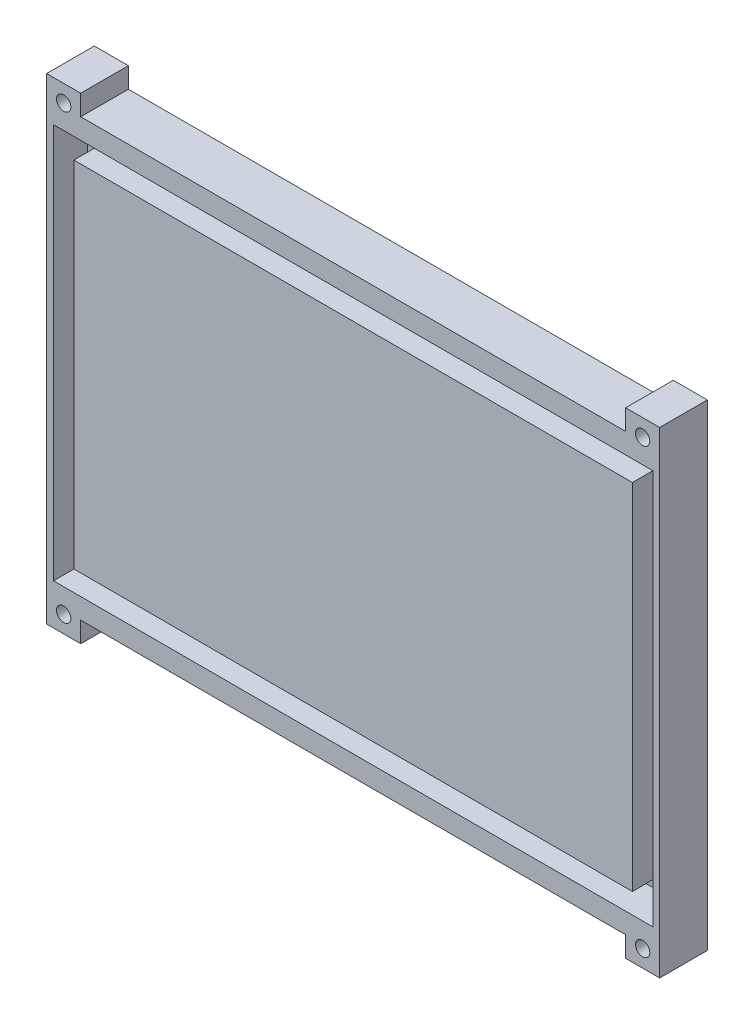
SolidWorks part; units mm, degrees
ref_plane "前基準面" through (0, 0, 0) normal (0, 0, 1) x (1, 0, 0)
ref_plane "上基準面" through (0, 0, 0) normal (0, 1, 0) x (1, 0, 0)
ref_plane "右基準面" through (0, 0, 0) normal (1, 0, 0) x (0, 0, -1)
sketch "草圖1" plane through (0, 0, 0) normal (0, 0, 1) x (1, 0, 0)
  line L1 (-89.0867, 42.9814) -> (10.9133, 42.9814)
  line L2 (-89.0867, 42.9814) -> (-89.0867, -27.0186)
  line L3 (-89.0867, -27.0186) -> (10.9133, -27.0186)
  line L4 (10.9133, 42.9814) -> (10.9133, -27.0186)
  dimension "D1" = 70
  dimension "D2" = 100
extrude "填料-伸長1" add sketch "草圖1" along normal blind 10 contours L4 L3 L2 L1
ref_plane "平面1" through (0, 0, 10) normal (0, 0, 1) x (1, 0, 0)
sketch "草圖6" plane through (0, 0, 10) normal (0, 0, 1) x (1, 0, 0)
  line L0 (-89.0867, 7.9814) -> (10.9133, 7.9814) construction
  line L1 (-89.0867, 42.9814) -> (-89.0867, -27.0186) construction
  line L2 (10.9133, 42.9814) -> (10.9133, -27.0186) construction
  line L3 (-39.0867, 42.9814) -> (-39.0867, -27.0186) construction
  line L4 (-89.0867, 42.9814) -> (10.9133, 42.9814) construction
  line L5 (-89.0867, -27.0186) -> (10.9133, -27.0186) construction
  line L6 (5.9133, 37.9814) -> (0.9133, 37.9814)
  line L7 (-84.0867, 42.9814) -> (-79.0867, 42.9814)
  line L8 (-84.0867, 42.9814) -> (-84.0867, 37.9814)
  line L9 (-84.0867, 37.9814) -> (-79.0867, 37.9814)
  line L10 (-79.0867, 42.9814) -> (-79.0867, 37.9814)
  line L11 (0.9133, 42.9814) -> (0.9133, 37.9814)
  line L12 (5.9133, 42.9814) -> (0.9133, 42.9814)
  line L13 (5.9133, 42.9814) -> (5.9133, 37.9814)
  line L14 (-84.0867, -22.0186) -> (-79.0867, -22.0186)
  line L15 (-79.0867, -27.0186) -> (-79.0867, -22.0186)
  line L16 (-84.0867, -27.0186) -> (-79.0867, -27.0186)
  line L17 (-84.0867, -27.0186) -> (-84.0867, -22.0186)
  line L18 (5.9133, -27.0186) -> (5.9133, -22.0186)
  line L19 (5.9133, -27.0186) -> (0.9133, -27.0186)
  line L20 (0.9133, -27.0186) -> (0.9133, -22.0186)
  line L21 (5.9133, -22.0186) -> (0.9133, -22.0186)
  dimension "D1" = 5
  dimension "D2" = 5
  dimension "D3" = 5
extrude "除料-伸長4" cut sketch "草圖6" against normal blind 5
ref_plane "平面2" through (0, 0, 0) normal (0, 0, -1) x (-1, 0, 0)
sketch "草圖7" plane through (0, 0, 0) normal (0, 0, -1) x (-1, 0, 0)
  line L0 (-10.9133, 7.9814) -> (89.0867, 7.9814) construction
  line L1 (-10.9133, 42.9814) -> (-10.9133, -27.0186) construction
  line L2 (89.0867, 42.9814) -> (89.0867, -27.0186) construction
  line L3 (39.0867, 42.9814) -> (39.0867, -27.0186) construction
  line L4 (89.0867, 42.9814) -> (-10.9133, 42.9814) construction
  line L5 (89.0867, -27.0186) -> (-10.9133, -27.0186) construction
  line L6 (84.0867, 37.9814) -> (79.0867, 37.9814)
  line L7 (-5.9133, 42.9814) -> (-0.9133, 42.9814)
  line L8 (-5.9133, 42.9814) -> (-5.9133, 37.9814)
  line L9 (-5.9133, 37.9814) -> (-0.9133, 37.9814)
  line L10 (-0.9133, 42.9814) -> (-0.9133, 37.9814)
  line L11 (79.0867, 42.9814) -> (79.0867, 37.9814)
  line L12 (84.0867, 42.9814) -> (79.0867, 42.9814)
  line L13 (84.0867, 42.9814) -> (84.0867, 37.9814)
  line L14 (84.0867, -27.0186) -> (84.0867, -22.0186)
  line L15 (84.0867, -27.0186) -> (79.0867, -27.0186)
  line L16 (79.0867, -27.0186) -> (79.0867, -22.0186)
  line L17 (84.0867, -22.0186) -> (79.0867, -22.0186)
  line L18 (-5.9133, -22.0186) -> (-0.9133, -22.0186)
  line L19 (-0.9133, -27.0186) -> (-0.9133, -22.0186)
  line L20 (-5.9133, -27.0186) -> (-0.9133, -27.0186)
  line L21 (-5.9133, -27.0186) -> (-5.9133, -22.0186)
  dimension "D1" = 5
  dimension "D2" = 5
  dimension "D3" = 5
extrude "除料-伸長5" cut sketch "草圖7" against normal blind 3
sketch "草圖8" plane through (0, 0, 0) normal (0, 0, -1) x (-1, 0, 0)
  line L0 (-10.9133, 7.9814) -> (89.0867, 7.9814) construction
  line L1 (-10.9133, 42.9814) -> (-10.9133, -27.0186) construction
  line L2 (89.0867, 42.9814) -> (89.0867, -27.0186) construction
  line L3 (39.0867, 42.9814) -> (39.0867, -27.0186) construction
  line L4 (79.0867, 42.9814) -> (-0.9133, 42.9814) construction
  line L5 (79.0867, -27.0186) -> (-0.9133, -27.0186) construction
  line L6 (-5.9133, 40.4814) -> (-0.9133, 40.4814) construction
  line L7 (-5.9133, 42.9814) -> (-5.9133, 37.9814) construction
  line L8 (-0.9133, 37.9814) -> (-0.9133, 42.9814) construction
  line L9 (-3.4133, 37.9814) -> (-3.4133, 42.9814) construction
  line L10 (-5.9133, 37.9814) -> (-0.9133, 37.9814) construction
  line L11 (-0.9133, 42.9814) -> (-5.9133, 42.9814) construction
  circle A0 centre (-3.4133, 40.4814) radius 1.05
  circle A1 centre (81.5867, 40.4814) radius 1.05
  circle A2 centre (81.5867, -24.5186) radius 1.05
  circle A3 centre (-3.4133, -24.5186) radius 1.05
  dimension "D1" = 2.1
  dimension "D2" = 2.1
  dimension "D3" = 2.1
  dimension "D4" = 2.1
extrude "除料-伸長6" cut sketch "草圖8" against normal blind 42
sketch "草圖10" plane through (0, 0, 0) normal (0, 0, 1) x (1, 0, 0)
  line L1 (-89.0867, 42.9814) -> (10.9133, 42.9814)
  line L2 (-89.0867, 42.9814) -> (-89.0867, -27.0186)
  line L3 (-89.0867, -27.0186) -> (10.9133, -27.0186)
  line L4 (10.9133, 42.9814) -> (10.9133, -27.0186)
extrude "除料-伸長7" cut sketch "草圖10" along normal blind 3
ref_plane "平面3" through (10.9133, 0, 0) normal (1, 0, 0) x (0, 0, -1)
sketch "草圖11" plane through (10.9133, 0, 0) normal (1, 0, 0) x (0, 0, -1)
  line L0 (-10, 38.5) -> (-10, -38.5) construction
  line L1 (-3, 42.9814) -> (-10, 42.9814)
  line L2 (-3, 42.9814) -> (-3, -27.0186)
  line L3 (-3, -27.0186) -> (-10, -27.0186)
  line L4 (-10, 42.9814) -> (-10, -27.0186)
  line L5 (-10, -27.0186) -> (-3, -27.0186) construction
extrude "除料-伸長8" cut sketch "草圖11" against normal blind 5
ref_plane "平面4" through (-89.0867, 0, 0) normal (-1, 0, 0) x (0, 0, 1)
sketch "草圖12" plane through (-89.0867, 0, 0) normal (-1, 0, 0) x (0, 0, 1)
  line L1 (3, 42.9814) -> (10, 42.9814)
  line L2 (3, 42.9814) -> (3, -27.0186)
  line L3 (3, -27.0186) -> (10, -27.0186)
  line L4 (10, 42.9814) -> (10, -27.0186)
extrude "除料-伸長9" cut sketch "草圖12" against normal blind 5
ref_plane "平面5" through (0, 0, 10) normal (0, 0, 1) x (1, 0, 0)
sketch "草圖13" plane through (0, 0, 10) normal (0, 0, 1) x (1, 0, 0)
  line L0 (-39.0867, 42.9814) -> (-39.0867, -27.0186) construction
  line L1 (-84.0867, 37.9814) -> (-79.0867, 37.9814)
  line L2 (-84.0867, 37.9814) -> (-84.0867, -22.0186)
  line L3 (-84.0867, -22.0186) -> (-79.0867, -22.0186)
  line L4 (-79.0867, 37.9814) -> (-79.0867, -22.0186)
  line L5 (-79.0867, 42.9814) -> (0.9133, 42.9814) construction
  line L6 (-79.0867, -27.0186) -> (0.9133, -27.0186) construction
  line L7 (5.9133, -22.0186) -> (0.9133, -22.0186)
  line L8 (0.9133, 37.9814) -> (0.9133, -22.0186)
  line L9 (5.9133, 37.9814) -> (0.9133, 37.9814)
  line L10 (5.9133, 37.9814) -> (5.9133, -22.0186)
sketch "草圖15" plane through (0, 0, 10) normal (0, 0, 1) x (1, 0, 0)
  line L0 (-84.0867, 7.9814) -> (0.9133, 7.9814) construction
  line L1 (-84.0867, 37.9814) -> (-84.0867, -22.0186) construction
  line L2 (0.9133, 37.9814) -> (0.9133, -22.0186) construction
  line L3 (-39.0867, 42.9814) -> (-39.0867, -27.0186) construction
  line L24 (-83.0867, 36.9814) -> (-83.0867, -21.0186)
  line L25 (-83.0867, 36.9814) -> (4.9133, 36.9814)
  line L26 (4.9133, 36.9814) -> (4.9133, -21.0186)
  line L27 (-80.0867, 33.9814) -> (1.9133, 33.9814)
  line L28 (-79.0867, 42.9814) -> (0.9133, 42.9814) construction
  line L29 (5.9133, 37.9814) -> (5.9133, -22.0186) construction
  line L30 (-80.0867, 33.9814) -> (-80.0867, -18.0186)
  line L31 (1.9133, 33.9814) -> (1.9133, -18.0186)
  line L32 (-83.0867, -21.0186) -> (4.9133, -21.0186)
  line L33 (-80.0867, -18.0186) -> (1.9133, -18.0186)
  point P19 (-83.0867, 7.9814)
  point P26 (-0.0867, 7.9814)
  point P27 (1.9133, 7.9814)
  point P29 (-80.0867, 7.9814)
  point P30 (-83.0867, 7.9814)
  point P32 (4.9133, 7.9814)
  point P33 (1.9133, 7.9814)
  point P35 (-80.0867, 7.9814)
  dimension "D1" = 3
  dimension "D2" = 9
  dimension "D3" = 3
  dimension "D4" = 1
  dimension "D5" = 1
  dimension "D6" = 3
  dimension "D7" = 6
extrude "除料-伸長12" cut sketch "草圖15" against normal blind 5
ref_plane "平面6" through (0, 0, 5) normal (0, 0, 1) x (1, 0, 0)
sketch "草圖16" plane through (0, 0, 5) normal (0, 0, 1) x (1, 0, 0)
  line L0 (-84.0867, 7.9814) -> (0.9133, 7.9814) construction
  line L1 (-84.0867, 37.9814) -> (-84.0867, -22.0186) construction
  line L2 (0.9133, 37.9814) -> (0.9133, -22.0186) construction
  line L3 (-39.0867, 42.9814) -> (-39.0867, -27.0186) construction
  line L4 (-84.0867, 42.9814) -> (-84.0867, 37.9814) construction
  line L5 (-79.0867, 37.9814) -> (-84.0867, 37.9814)
  line L6 (-79.0867, 37.9814) -> (-79.0867, 42.9814)
  line L7 (-79.0867, 42.9814) -> (-84.0867, 42.9814)
  line L8 (-84.0867, 37.9814) -> (-84.0867, 42.9814)
  line L9 (0.9133, 42.9814) -> (5.9133, 42.9814)
  line L10 (5.9133, 37.9814) -> (5.9133, 42.9814)
  line L11 (0.9133, 37.9814) -> (5.9133, 37.9814)
  line L12 (0.9133, 37.9814) -> (0.9133, 42.9814)
  line L13 (0.9133, -22.0186) -> (0.9133, -27.0186)
  line L14 (0.9133, -22.0186) -> (5.9133, -22.0186)
  line L15 (5.9133, -22.0186) -> (5.9133, -27.0186)
  line L16 (0.9133, -27.0186) -> (5.9133, -27.0186)
  line L17 (-79.0867, -27.0186) -> (-84.0867, -27.0186)
  line L18 (-84.0867, -22.0186) -> (-84.0867, -27.0186)
  line L19 (-79.0867, -22.0186) -> (-84.0867, -22.0186)
  line L20 (-79.0867, -22.0186) -> (-79.0867, -27.0186)
  circle A0 centre (-81.5867, 40.4814) radius 1.05
  circle A1 centre (3.4133, 40.4814) radius 1.05
  circle A2 centre (3.4133, -24.5186) radius 1.05
  circle A3 centre (-81.5867, -24.5186) radius 1.05
extrude "填料-伸長2" add sketch "草圖16" along normal blind 5
sketch "草圖18" plane through (0, 0, 10) normal (0, 0, 1) x (1, 0, 0)
  line L0 (-84.0867, 7.9814) -> (5.9133, 7.9814) construction
  line L1 (-84.0867, 37.9814) -> (-84.0867, -22.0186) construction
  line L2 (5.9133, 37.9814) -> (5.9133, -22.0186) construction
  line L3 (-84.0867, 42.9814) -> (5.9133, 42.9814) construction
  line L4 (-79.0867, 42.9814) -> (0.9133, 42.9814)
  line L5 (-79.0867, 42.9814) -> (-79.0867, 39.9814)
  line L6 (-79.0867, 39.9814) -> (0.9133, 39.9814)
  line L7 (0.9133, 42.9814) -> (0.9133, 39.9814)
  line L8 (4.9133, 36.9814) -> (-83.0867, 36.9814) construction
  line L9 (-79.0867, -24.0186) -> (0.9133, -24.0186)
  line L10 (0.9133, -27.0186) -> (0.9133, -24.0186)
  line L11 (-79.0867, -27.0186) -> (0.9133, -27.0186)
  line L12 (-79.0867, -27.0186) -> (-79.0867, -24.0186)
  dimension "D1" = 80
  dimension "D2" = 5
  dimension "D3" = 5
  dimension "D4" = 3
extrude "除料-伸長13" cut sketch "草圖18" against normal blind 10
